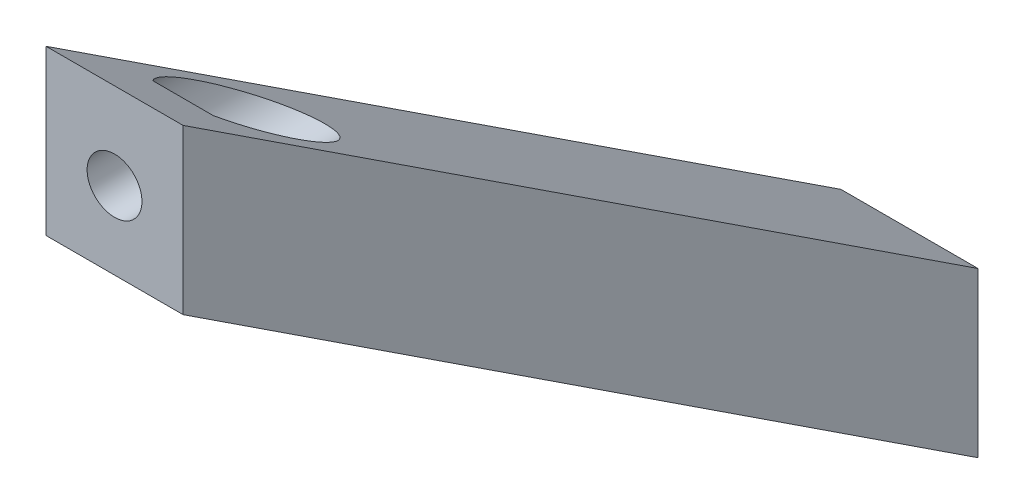
SolidWorks part; units mm, degrees
ref_plane "Front Plane" through (0, 0, 0) normal (0, 0, 1) x (1, 0, 0)
ref_plane "Top Plane" through (0, 0, 0) normal (0, 1, 0) x (1, 0, 0)
ref_plane "Right Plane" through (0, 0, 0) normal (1, 0, 0) x (0, 0, -1)
sketch "Sketch1" plane through (0, 0, 0) normal (1, 0, 0) x (0, 0, -1)
  line L6 (0, 124.2951) -> (191.4955, -1.3028)
  line L7 (116, 24.2951) -> (116, 48.2131)
  line L8 (0, 100.377) -> (116, 24.2951)
  line L9 (0, 124.2951) -> (0, 100.377)
  point P6 (116, 24.2951)
  point P12 (0, 100.377)
  point P15 (0, 124.2951)
  dimension "D1" = 116
  dimension "D2" = 100
extrude "Boss-Extrude1" add sketch "Sketch1" along normal blind 20 contours L6 L9 L8 L7
sketch "Sketch2" plane through (0, 0, 0) normal (0, 0, 1) x (1, 0, 0)
  line L0 (20, 124.2951) -> (20, 100.377) construction
  circle A2 centre (10, 111.6802) radius 4
  dimension "D1" = 10
  dimension "D3" = 8
extrude "Cut-Extrude5" cut sketch "Sketch2" along direction (0, 0, -1) on the side against the normal through all contours A2
sketch "Sketch5" plane through (0, 0, 0) normal (0, 0, 1) x (1, 0, 0)
  circle A0 centre (10, 111.6802) radius 7.5
  dimension "D1" = 15
extrude "Cut-Extrude6" cut sketch "Sketch5" against normal through all from offset 10 offset against normal yes
sketch "Sketch6" plane through (0, 0, -116) normal (0, 0, -1) x (-1, 0, 0)
  circle A0 centre (-10, 36.9099) radius 4
  dimension "D1" = 8
extrude "Cut-Extrude7" cut sketch "Sketch6" against normal through all
sketch "Sketch7" plane through (0, 0, -116) normal (0, 0, -1) x (-1, 0, 0)
  circle A0 centre (-10, 36.9099) radius 7.5
  dimension "D1" = 15
extrude "Cut-Extrude8" cut sketch "Sketch7" against normal through all from offset 10
